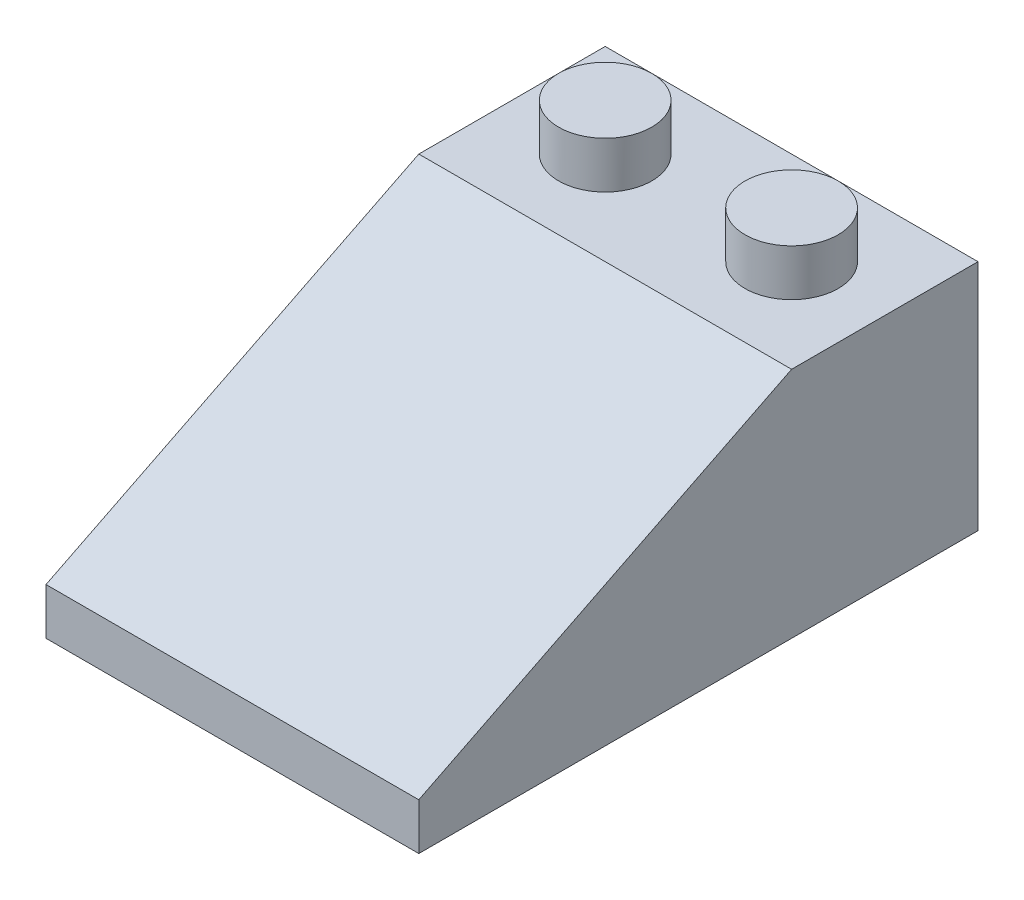
SolidWorks part; units mm, degrees
ref_plane "Front Plane" through (0, 0, 0) normal (0, 0, 1) x (1, 0, 0)
ref_plane "Top Plane" through (0, 0, 0) normal (0, 1, 0) x (1, 0, 0)
ref_plane "Right Plane" through (0, 0, 0) normal (1, 0, 0) x (0, 0, -1)
sketch "Sketch1" plane through (0, 0, 0) normal (1, 0, 0) x (0, 0, -1)
  line L0 (0, 0) -> (0, -2)
  line L1 (0, -2) -> (24, -2)
  line L2 (24, -2) -> (24, 8)
  line L3 (24, 8) -> (16, 8)
  line L4 (16, 8) -> (0, 0)
  dimension "D1" = 2
  dimension "D2" = 24
  dimension "D3" = 10
  dimension "D4" = 8
extrude "Boss-Extrude1" add sketch "Sketch1" along normal mid plane 16
sketch "Sketch2" plane through (0, 8, 0) normal (0, 1, 0) x (1, 0, 0)
  line L0 (0, 24) -> (0, 16) construction
  line L1 (8, 24) -> (-8, 24) construction
  line L2 (8, 16) -> (-8, 16) construction
  line L3 (-8, 24) -> (-8, 16) construction
  circle A0 centre (-4, 20) radius 2
  circle A1 centre (4, 20) radius 2
  dimension "D1" = 4
  dimension "D2" = 4
  dimension "D3" = 4
extrude "Boss-Extrude2" add sketch "Sketch2" along normal blind 2
shell "Shell1" thickness 1
sketch "Sketch3" plane through (0, 0, 0) normal (0, 1, 0) x (1, 0, 0)
  line L0 (-8, 16) -> (-8, 0) construction
  line L1 (8, 0) -> (-8, 0) construction
  line L2 (-8, 12) -> (8, 12) construction
  line L3 (-8, 0) -> (-8, 24) construction
  line L4 (8, 0) -> (8, 24) construction
  circle A0 centre (0, 8) radius 1.7
  circle A1 centre (0, 8) radius 2.7
  circle A2 centre (0, 16) radius 1.7
  circle A3 centre (0, 16) radius 2.7
  dimension "D1" = 5.4
  dimension "D2" = 3.4
  dimension "D3" = 8
  dimension "D4" = 8
extrude "Boss-Extrude3" add sketch "Sketch3" along normal up to next
